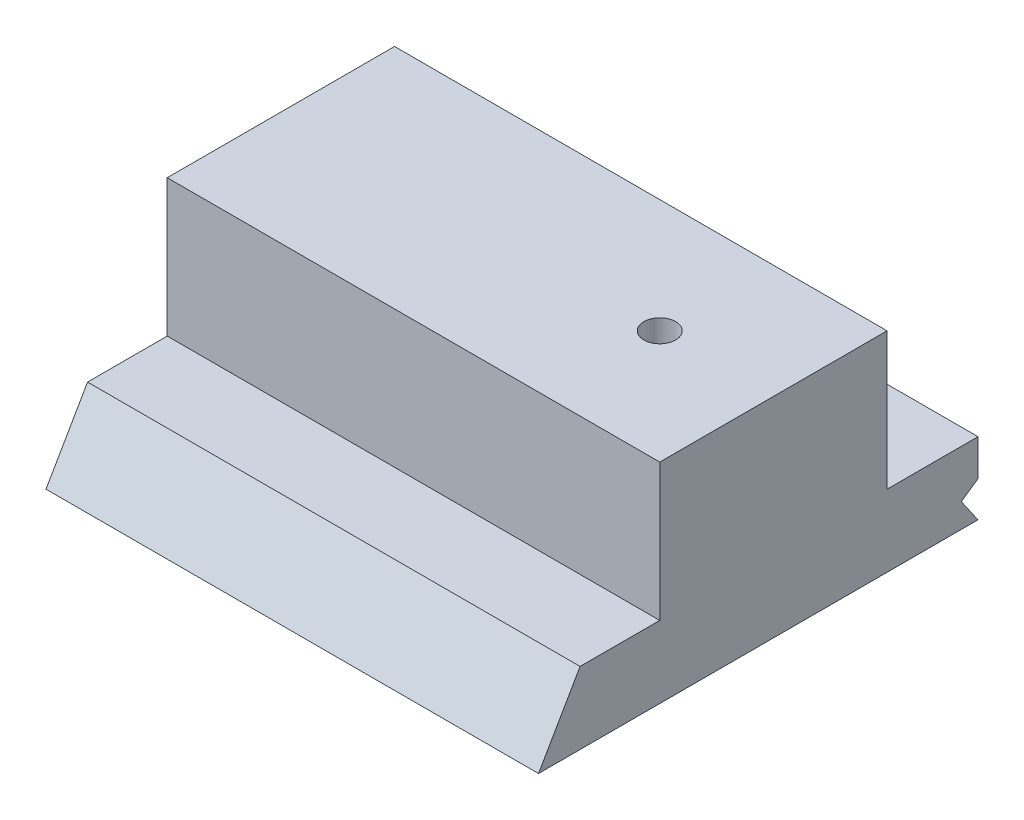
SolidWorks part; units mm, degrees
material "Chrome Stainless Steel"
ref_plane "Front Plane" through (0, 0, 0) normal (0, 0, 1) x (1, 0, 0)
ref_plane "Top Plane" through (0, 0, 0) normal (0, 1, 0) x (1, 0, 0)
ref_plane "Right Plane" through (0, 0, 0) normal (1, 0, 0) x (0, 0, -1)
sketch "Sketch1" plane through (0, 0, 0) normal (0, 1, 0) x (1, 0, 0)
  line L1 (0, 0) -> (65, 0)
  line L2 (0, 0) -> (0, 58)
  line L3 (0, 58) -> (65, 58)
  line L4 (65, 0) -> (65, 58)
  dimension "D1" = 65
  dimension "D2" = 58
extrude "Extrude1" add sketch "Sketch1" along normal blind 9.5
sketch "Sketch2" plane through (65, 0, 0) normal (1, 0, 0) x (0, 0, -1)
  line L0 (0, 0) -> (5.4848, 9.5)
  line L1 (0, 9.5) -> (58, 9.5) construction
  line L2 (5.4848, 9.5) -> (0, 9.5)
  line L3 (0, 9.5) -> (0, 0)
  line L4 (0, 0) -> (58, 0) construction
  dimension "D1" = 60
extrude "Extrude2" cut sketch "Sketch2" against normal through all
sketch "Sketch3" plane through (65, 0, 0) normal (1, 0, 0) x (0, 0, -1)
  line L0 (58, 0) -> (58, 4.7)
  line L2 (58, 0) -> (55.8, 3.1761)
  line L3 (55.8, 3.1761) -> (58, 4.7)
  dimension "D1" = 4.7
  dimension "D2" = 2.2
extrude "Extrude3" cut sketch "Sketch3" against normal through all
sketch "Sketch4" plane through (0, 0, 0) normal (-1, 0, 0) x (0, 0, 1)
  line L0 (-58, 9.5) -> (-5.4848, 9.5) construction
  line L1 (-46, 9.5) -> (-16, 9.5)
  line L2 (-46, 9.5) -> (-46, 27.6)
  line L3 (-46, 27.6) -> (-16, 27.6)
  line L4 (-16, 9.5) -> (-16, 27.6)
  line L5 (-58, 9.5) -> (-58, 4.7) construction
  dimension "D1" = 12
  dimension "D2" = 30
  dimension "D3" = 18.1
extrude "Extrude4" add sketch "Sketch4" against normal up to surface (65 mm away) up to face at (65, 4.4794, -39.2141)
sketch "Sketch5" plane through (0, 27.6, 0) normal (0, 1, 0) x (1, 0, 0)
  line L0 (65, 46) -> (65, 16) construction
  line L1 (65, 46) -> (0, 46) construction
  circle A0 centre (50, 31) radius 2.1
  dimension "D1" = 15
  dimension "D2" = 4.2
  dimension "D3" = 15
extrude "Extrude5" cut sketch "Sketch5" against normal through all
sketch "Sketch6" plane through (0, 0, 0) normal (0, -1, 0) x (1, 0, 0)
  circle A0 centre (50, -31) radius 4
  dimension "D1" = 8
extrude "Extrude6" cut sketch "Sketch6" against normal blind 20
